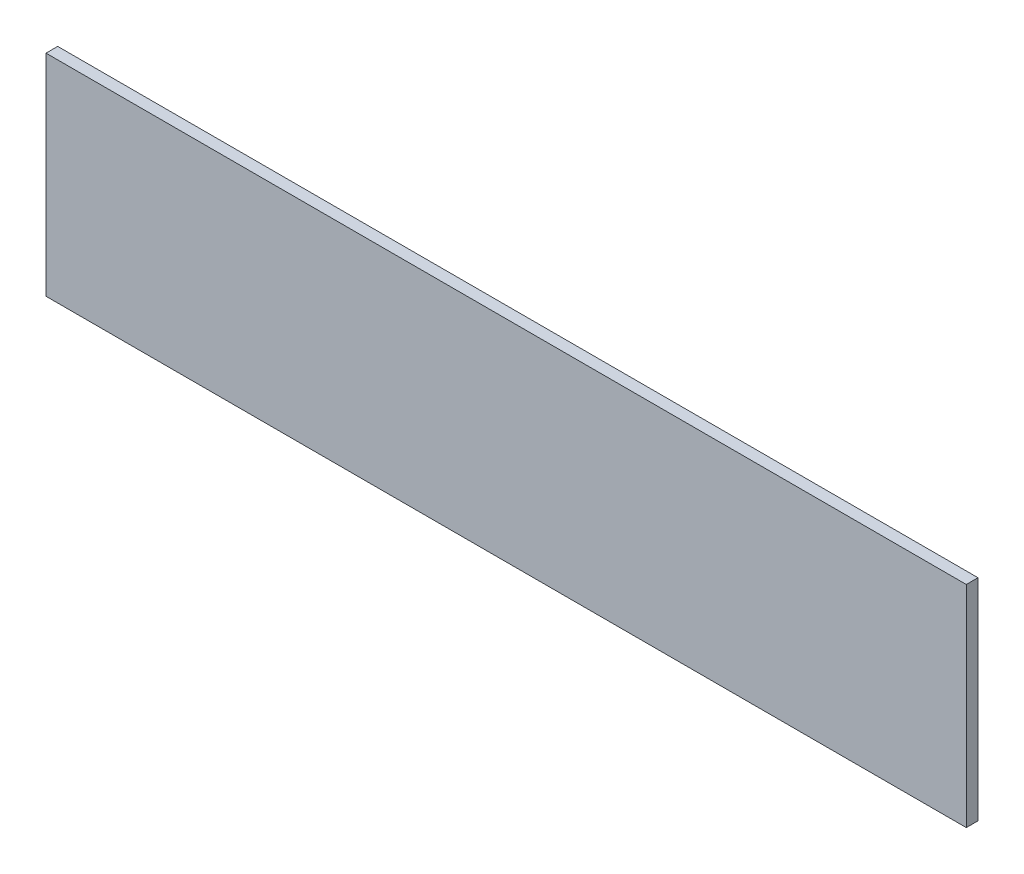
SolidWorks part; units mm, degrees
material "ABS PC"
ref_plane "Front Plane" through (0, 0, 0) normal (0, 0, 1) x (1, 0, 0)
ref_plane "Top Plane" through (0, 0, 0) normal (0, 1, 0) x (1, 0, 0)
ref_plane "Right Plane" through (0, 0, 0) normal (1, 0, 0) x (0, 0, -1)
sketch "Sketch1" plane through (0, 0, 0) normal (0, 0, 1) x (1, 0, 0)
  line L4 (-167.2098, -170.7686) -> (-167.2098, -184.4846)
  line L5 (-167.2098, -184.4846) -> (-107.2658, -184.4846)
  line L6 (-107.2658, -184.4846) -> (-107.2658, -170.7686)
  line L7 (-107.2658, -170.7686) -> (-167.2098, -170.7686)
  line L8 (-167.2098, -170.7686) -> (-167.2098, -184.4846)
  line L9 (-167.2098, -184.4846) -> (-107.2658, -184.4846)
  line L10 (-107.2658, -184.4846) -> (-107.2658, -170.7686)
  line L11 (-107.2658, -170.7686) -> (-167.2098, -170.7686)
  dimension "D1" = 0
extrude "Boss-Extrude1" add sketch "Sketch1" along normal blind 0.762
